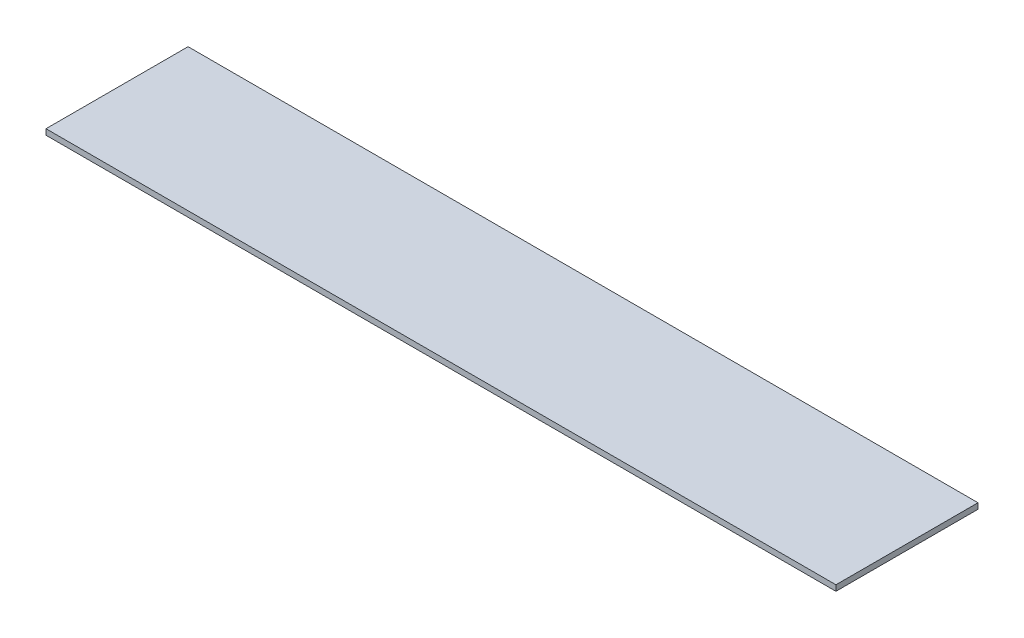
SolidWorks part; units mm, degrees
ref_plane "Front Plane" through (0, 0, 0) normal (0, 0, 1) x (1, 0, 0)
ref_plane "Top Plane" through (0, 0, 0) normal (0, 1, 0) x (1, 0, 0)
ref_plane "Right Plane" through (0, 0, 0) normal (1, 0, 0) x (0, 0, -1)
sketch "Sketch2" plane through (0, 0, 0) normal (0, 1, 0) x (1, 0, 0)
  line L1 (0, 0) -> (278, 0)
  line L2 (0, 0) -> (0, 50)
  line L3 (0, 50) -> (278, 50)
  line L4 (278, 0) -> (278, 50)
  dimension "D1" = 278
  dimension "D2" = 50
extrude "Boss-Extrude1" add sketch "Sketch2" along normal blind 2
